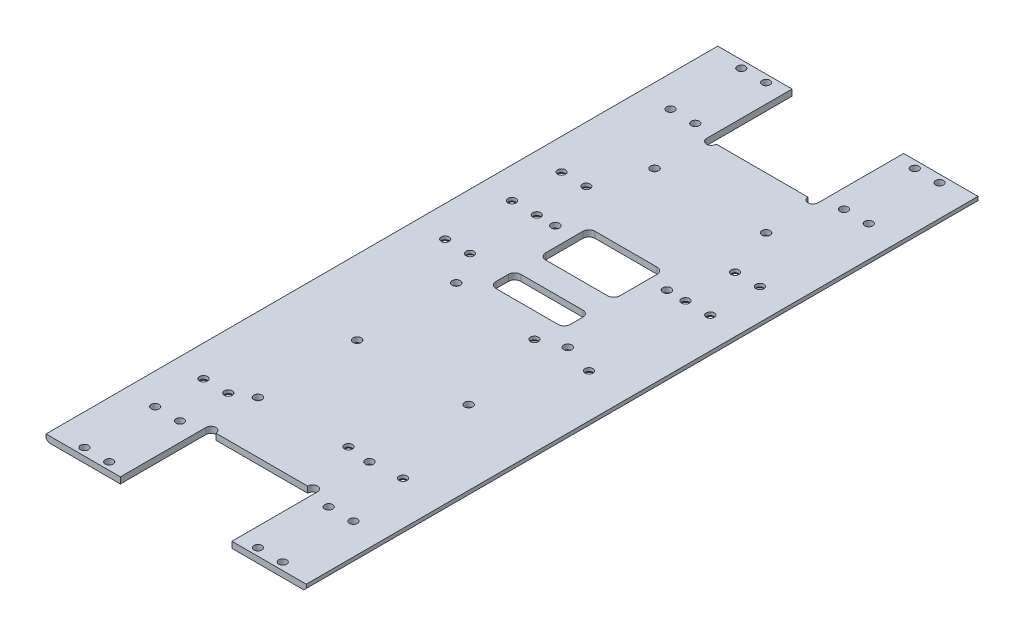
SolidWorks part; units mm, degrees
material "Thornel Mat VMA"
ref_plane "前视基准面" through (0, 0, 0) normal (0, 0, 1) x (1, 0, 0)
ref_plane "上视基准面" through (0, 0, 0) normal (0, 1, 0) x (1, 0, 0)
ref_plane "右视基准面" through (0, 0, 0) normal (1, 0, 0) x (0, 0, -1)
sketch "草图1" plane through (0, 0, 0) normal (0, 1, 0) x (1, 0, 0)
  line L6 (-52.5, -135.5) -> (52.5, -135.5)
  line L7 (52.5, -135.5) -> (52.5, 135.5)
  line L8 (-52.5, 135.5) -> (52.5, 135.5)
  line L9 (-52.5, -135.5) -> (-52.5, 135.5)
  point P8 (-50, 0)
extrude "凸台-拉伸1" add sketch "草图1" along normal blind 2.5
sketch "草图2" plane through (0, 2.5, 0) normal (0, 1, 0) x (1, 0, 0)
  circle A20 centre (13, -3.95) radius 1.6
  circle A21 centre (35, -3.95) radius 1.6
  circle A24 centre (35, -78.95) radius 1.6
  circle A25 centre (13, -78.95) radius 1.6
extrude "切除-拉伸1" cut sketch "草图2" against normal blind 10
chamfer "倒角4" distance 1 angle 45 2 edges at (52.5, 0, 0) (-52.5, 0, 0)
sketch "草图3" plane through (0, 0, 0) normal (0, -1, 0) x (1, 0, 0)
  line L0 (-22.5, 100.95) -> (22.5, 100.95)
  line L2 (-51.5, 135.5) -> (51.5, 135.5) construction
  line L3 (1.375, 0) -> (-1.375, 0) construction
  line L4 (22.5, 100.95) -> (22.5, 135.5)
  line L5 (22.5, 135.5) -> (-22.5, 135.5)
  line L6 (-22.5, 135.5) -> (-22.5, 100.95)
  line L7 (-22.5, -135.5) -> (-22.5, -100.95)
  line L8 (22.5, -135.5) -> (-22.5, -135.5)
  line L9 (22.5, -100.95) -> (22.5, -135.5)
  line L10 (-22.5, -100.95) -> (22.5, -100.95)
extrude "切除-拉伸2" cut sketch "草图3" against normal blind 10
sketch "草图4" plane through (0, 0, 0) normal (0, -1, 0) x (1, 0, 0)
  line L0 (0, -1.375) -> (0, 1.375) construction
  line L1 (22.5, -100.95) -> (-22.5, -100.95) construction
  line L2 (1.375, 0) -> (-1.375, 0) construction
  circle A0 centre (20.5, -100.95) radius 2
  circle A1 centre (-20.5, -100.95) radius 2
  circle A2 centre (-20.5, 100.95) radius 2
  circle A3 centre (20.5, 100.95) radius 2
extrude "切除-拉伸3" cut sketch "草图4" against normal blind 10
sketch "草图5" plane through (0, 2.5, 0) normal (0, 1, 0) x (1, 0, 0)
  line L0 (0, -1.375) -> (0, 1.375) construction
  line L3 (-1.375, 0) -> (1.375, 0) construction
  circle A0 centre (-40, 103.95) radius 1.6
  circle A1 centre (-30, 103.95) radius 1.6
  circle A4 centre (-40, 132.5) radius 1.6
  circle A5 centre (-30, 132.5) radius 1.6
  circle A6 centre (30, 132.5) radius 1.6
  circle A7 centre (40, 132.5) radius 1.6
  circle A8 centre (30, 103.95) radius 1.6
  circle A9 centre (40, 103.95) radius 1.6
  circle A10 centre (40, -103.95) radius 1.6
  circle A11 centre (30, -103.95) radius 1.6
  circle A12 centre (40, -132.5) radius 1.6
  circle A13 centre (30, -132.5) radius 1.6
  circle A14 centre (-30, -132.5) radius 1.6
  circle A15 centre (-40, -132.5) radius 1.6
  circle A16 centre (-30, -103.95) radius 1.6
  circle A17 centre (-40, -103.95) radius 1.6
extrude "切除-拉伸4" cut sketch "草图5" against normal blind 10
sketch "草图6" plane through (0, 2.5, 0) normal (0, 1, 0) x (1, 0, 0)
  line L0 (0, -1.375) -> (0, 1.375) construction
  circle A0 centre (40, 60) radius 1.6
  circle A1 centre (30, 60) radius 1.6
  circle A2 centre (40, 40) radius 1.6
  circle A3 centre (30, 40) radius 1.6
  circle A4 centre (-30, 40) radius 1.6
  circle A5 centre (-40, 40) radius 1.6
  circle A6 centre (-30, 60) radius 1.6
  circle A7 centre (-40, 60) radius 1.6
  circle A8 centre (-30, -84.45) radius 1.6
  circle A9 centre (-40, -84.45) radius 1.6
  circle A10 centre (-30, 13.05) radius 1.6
  circle A11 centre (-40, 13.05) radius 1.6
  dimension "D1" = 2
extrude "切除-拉伸5" cut sketch "草图6" against normal blind 10
sketch "草图7" plane through (0, 2.5, 0) normal (0, 1, 0) x (1, 0, 0)
  line L0 (0, -1.375) -> (0, 1.375) construction
  line L2 (-1.375, 0) -> (1.375, 0) construction
  circle A0 centre (-22.5, 0) radius 1.65
  circle A2 centre (-22.5, -40) radius 1.65
  circle A4 centre (-22.5, -80) radius 1.65
  circle A5 centre (-22.5, -20) radius 1.65 [skipped]
  circle A6 centre (-22.5, -60) radius 1.65 [skipped]
  circle A7 centre (22.5, -80) radius 1.65
  circle A8 centre (22.5, -40) radius 1.65
  circle A9 centre (22.5, 0) radius 1.65
  circle A10 centre (22.5, 40) radius 1.65
  circle A11 centre (22.5, 80) radius 1.65
  circle A12 centre (-22.5, 80) radius 1.65
  circle A13 centre (-22.5, 40) radius 1.65
  dimension "D1" = 5
extrude "切除-拉伸6" cut sketch "草图7" against normal blind 2
sketch "草图8" plane through (0, 2.5, 0) normal (0, 1, 0) x (1, 0, 0)
  line L0 (0, -1.375) -> (0, 1.375) construction
  circle A0 centre (-22.5, 80) radius 1.55
  circle A1 centre (-22.5, 40) radius 1.55
  circle A2 centre (-22.5, 0) radius 1.55
  circle A3 centre (-22.5, -40) radius 1.55
  circle A4 centre (-22.5, -80) radius 1.55
  circle A5 centre (22.5, -80) radius 1.55
  circle A6 centre (22.5, -40) radius 1.55
  circle A7 centre (22.5, 0) radius 1.55
  circle A8 centre (22.5, 40) radius 1.55
  circle A9 centre (22.5, 80) radius 1.55
  dimension "D1" = 5
extrude "切除-拉伸7" cut sketch "草图8" against normal up to next
chamfer "倒角6" distance 1.2 angle 45 16 edges at (40, 0, -61.6) (30, 0, -61.6) (40, 0, -41.6) (30, 0, -41.6) (-30, 0, -61.6) (-40, 0, -61.6) (-30, 0, -41.6) (-40, 0, -41.6) (-30, 0, 82.85) (-40, 0, 82.85) (-30, 0, -14.65) (-40, 0, -14.65) (35, 0, 2.35) (13, 0, 2.35) (35, 0, 77.35) (13, 0, 77.35)
sketch "草图9" plane through (0, 0, 0) normal (0, -1, 0) x (1, 0, 0)
  line L0 (-15, -26.05) -> (-15, -46.05)
  line L1 (-15, -16.05) -> (15, -16.05)
  line L3 (15, -6.05) -> (-15, -6.05)
  line L4 (-15, -6.05) -> (-15, -16.05)
  line L5 (15, -6.05) -> (15, -16.05)
  line L6 (-15, -46.05) -> (15, -46.05)
  line L8 (15, -26.05) -> (-15, -26.05)
  line L11 (15, -46.05) -> (15, -26.05)
  line L13 (-15, -36.05) -> (15, -36.05) [skipped]
  line L14 (-15, -26.05) -> (-15, -36.05) [skipped]
  line L15 (15, -26.05) -> (15, -36.05) [skipped]
  dimension "D1" = 2
extrude "切除-拉伸8" cut sketch "草图9" against normal blind 12 contours L5 L3 L4 L1 | L11 L8 L0 L6
fillet "圆角1" radius 2.5 8 edges at (15, 1.25, -16.05) (15, 1.25, -6.05) (-15, 1.25, -16.05) (-15, 1.25, -6.05) (-15, 1.25, -46.05) (15, 1.25, -46.05) (15, 1.25, -26.05) (-15, 1.25, -26.05)
